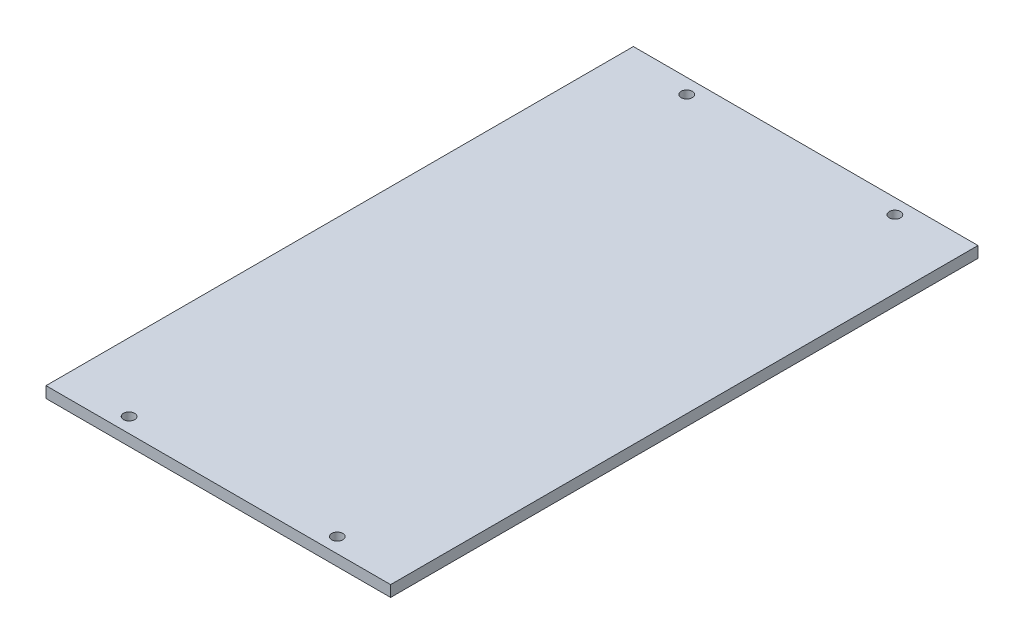
SolidWorks part; units mm, degrees
ref_plane "Front Plane" through (0, 0, 0) normal (0, 0, 1) x (1, 0, 0)
ref_plane "Top Plane" through (0, 0, 0) normal (0, 1, 0) x (1, 0, 0)
ref_plane "Right Plane" through (0, 0, 0) normal (1, 0, 0) x (0, 0, -1)
ref_plane "Plane1" through (0, 3, 0) normal (0, 1, 0) x (1, 0, 0)
sketch "Sketch1" plane through (0, 3, 0) normal (0, 1, 0) x (1, 0, 0)
  line L0 (-46.35, 79) -> (-46.35, -79)
  line L1 (-46.35, -79) -> (46.35, -79)
  line L2 (46.35, -79) -> (46.35, 79)
  line L3 (46.35, 79) -> (-46.35, 79)
  circle A0 centre (28, -75) radius 1.5
  circle A1 centre (28, 75) radius 1.5
  circle A2 centre (-28, 75) radius 1.5
  circle A3 centre (-28, -75) radius 1.5
extrude "Boss-Extrude1" add sketch "Sketch1" against normal blind 3
